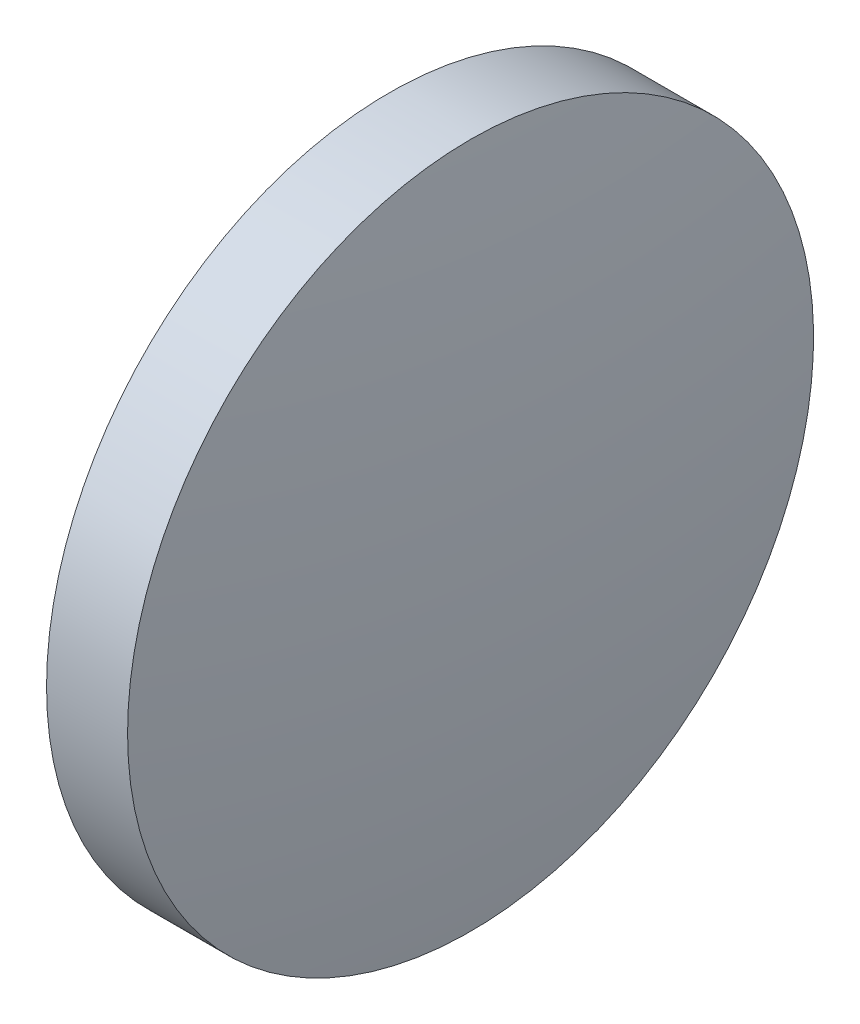
SolidWorks part; units mm, degrees
ref_plane "前视基准面" through (0, 0, 0) normal (0, 0, 1) x (1, 0, 0)
ref_plane "上视基准面" through (0, 0, 0) normal (0, 1, 0) x (1, 0, 0)
ref_plane "右视基准面" through (0, 0, 0) normal (1, 0, 0) x (0, 0, -1)
sketch "草图1" plane through (0, 0, 0) normal (0, 0, 1) x (1, 0, 0)
  line L0 (110.1654, 65.2336) -> (128.9614, 65.2336) construction
  line L1 (115.7736, 65.2336) -> (115.7736, 77.9336)
  line L2 (115.7736, 77.9336) -> (118.7739, 77.9336)
  line L3 (119.6566, 65.2336) -> (115.7736, 65.2336)
  arc A0 (119.6566, 65.2336) -> (118.7739, 77.9336) centre (27.8566, 65.2336) ccw
  dimension "D1" = 91.8
  dimension "D2" = 3.883
revolve "旋转1" add sketch "草图1" angle 360 about L0
